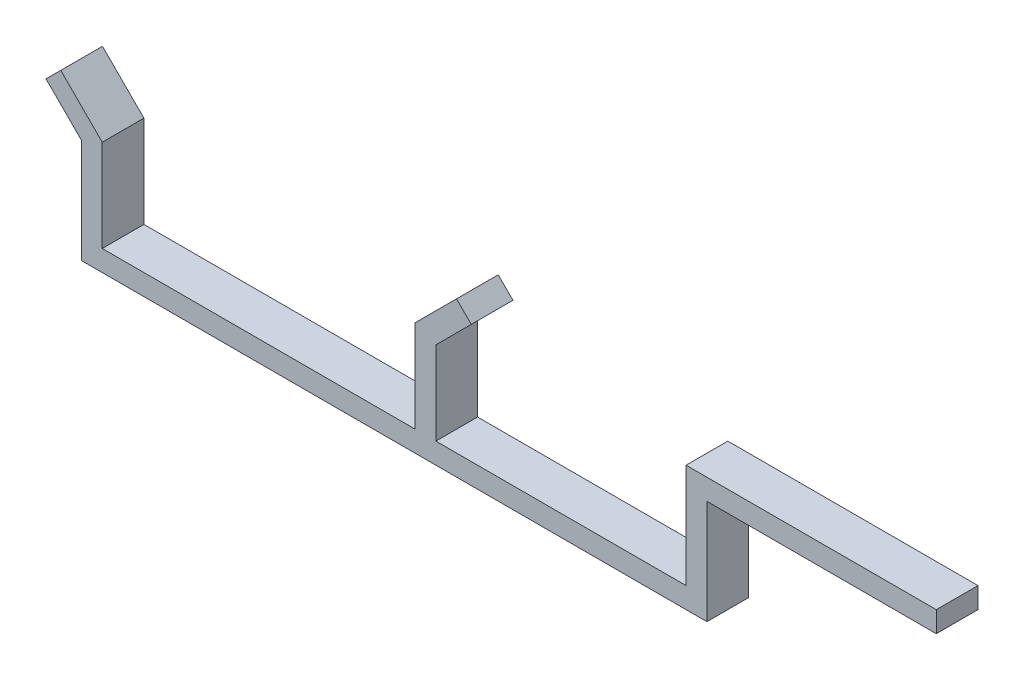
SolidWorks part; units mm, degrees
ref_plane "Front Plane" through (0, 0, 0) normal (0, 0, 1) x (1, 0, 0)
ref_plane "Top Plane" through (0, 0, 0) normal (0, 1, 0) x (1, 0, 0)
ref_plane "Right Plane" through (0, 0, 0) normal (1, 0, 0) x (0, 0, -1)
sketch "Sketch1" plane through (0, 0, 0) normal (0, 0, 1) x (1, 0, 0)
  line L0 (-42.5, 8.6352) -> (-42.5, -16.3648)
  line L1 (-42.5, -16.3648) -> (107.5, -16.3648)
  line L3 (-37.5, 8.6352) -> (-37.5, -11.3648)
  line L4 (-37.5, -11.3648) -> (37.5, -11.3648)
  line L5 (102.5, -11.3648) -> (102.5, 13.6352)
  line L8 (37.5, -11.3648) -> (37.5, 8.6352)
  line L9 (42.5, -11.3648) -> (42.5, 8.6352)
  line L11 (42.5, -11.3648) -> (102.5, -11.3648)
  line L12 (102.5, 13.6352) -> (162.5, 13.6352)
  line L13 (-42.5, 8.6352) -> (-50.9853, 17.1205)
  line L14 (-37.5, 8.6352) -> (-37.5, 10.7063)
  line L15 (162.5, 13.6352) -> (162.5, 8.6352)
  line L16 (162.5, 8.6352) -> (107.5, 8.6352)
  line L17 (107.5, 8.6352) -> (107.5, -16.3648)
  line L27 (-37.5, 10.7063) -> (-47.4497, 20.6561)
  line L28 (-50.9853, 17.1205) -> (-47.4497, 20.6561)
  line L31 (0, 32.5116) -> (0, -30.2485) construction
  line L32 (37.5, 8.6352) -> (37.5, 10.7063)
  line L33 (42.5, 8.6352) -> (50.9853, 17.1205)
  line L34 (50.9853, 17.1205) -> (47.4497, 20.6561)
  line L35 (37.5, 10.7063) -> (47.4497, 20.6561)
  point P31 (0, -11.3648)
  dimension "D3" = 150
  dimension "D4" = 60
  dimension "D5" = 20
  dimension "D6" = 20
  dimension "D1" = 25
  dimension "D2" = 5
  dimension "D7" = 25
  dimension "D8" = 12
extrude "Boss-Extrude1" add sketch "Sketch1" along normal blind 10
sketch "Sketch2" plane through (0, 13.6352, 0) normal (0, 1, 0) x (1, 0, 0)
  line L0 (162.5, 0) -> (102.5, 0) construction
  circle A0 centre (132.5, -5) radius 3
  dimension "D1" = 6
  dimension "D2" = 5
